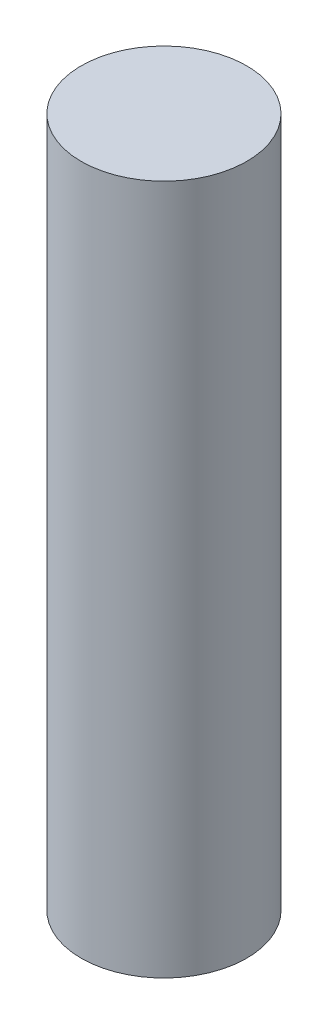
SolidWorks part; units mm, degrees
ref_plane "Front Plane" through (0, 0, 0) normal (0, 0, 1) x (1, 0, 0)
ref_plane "Top Plane" through (0, 0, 0) normal (0, 1, 0) x (1, 0, 0)
ref_plane "Right Plane" through (0, 0, 0) normal (1, 0, 0) x (0, 0, -1)
sketch "Sketch1" plane through (0, 0, 0) normal (0, 1, 0) x (1, 0, 0)
  circle A0 centre (0, 0) radius 6
  dimension "D1" = 12
extrude "Boss-Extrude1" add sketch "Sketch1" along normal mid plane 50
ref_plane "Plane1" through (0, -12.7594, 0) normal (0, 1, 0) x (1, 0, 0)
sketch "Sketch2" plane through (0, -12.7594, 0) normal (0, 1, 0) x (1, 0, 0)
  line L1 (0, 11.1429) -> (-9.65, 5.5714)
  line L2 (-9.65, 5.5714) -> (-9.65, -5.5714)
  line L3 (-9.65, -5.5714) -> (0, -11.1429)
  line L4 (0, -11.1429) -> (9.65, -5.5714)
  line L5 (9.65, -5.5714) -> (9.65, 5.5714)
  line L6 (9.65, 5.5714) -> (0, 11.1429)
  circle A0 centre (0, 0) radius 9.65 construction
  circle A1 centre (0, 0) radius 6
  circle A2 centre (0, 0) radius 6 construction
  dimension "D1" = 19.3
